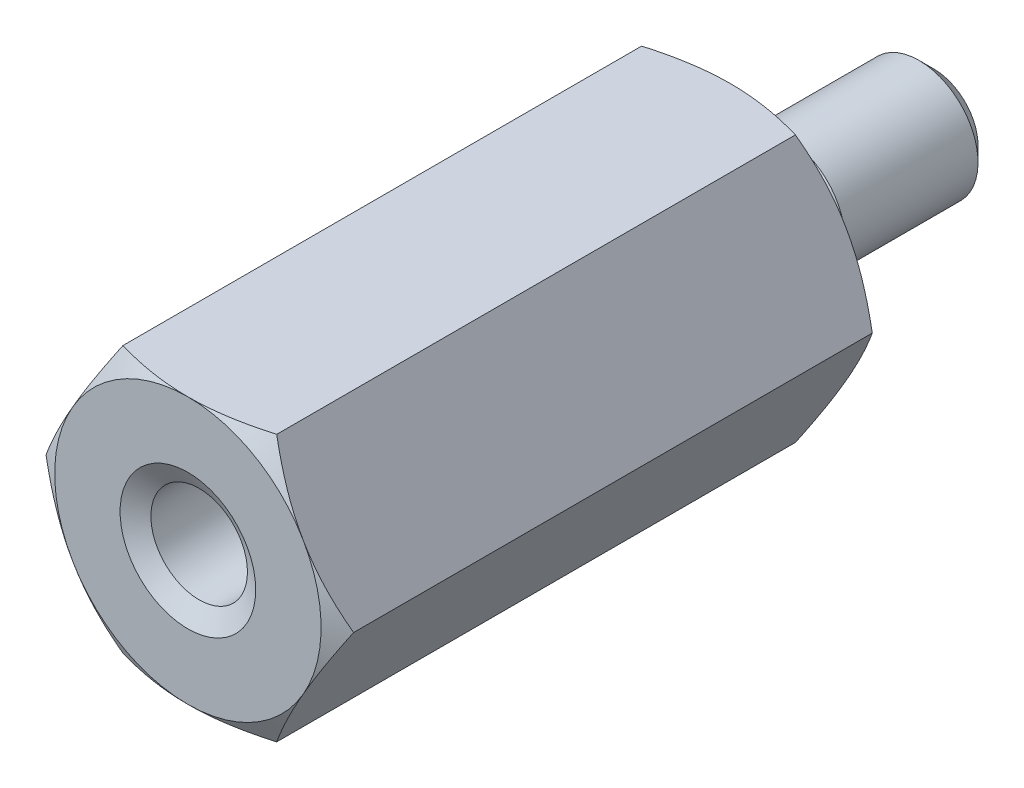
SolidWorks part; units mm, degrees
material "Plain Carbon Steel"
ref_plane "Front" through (0, 0, 0) normal (0, 0, 1) x (1, 0, 0)
ref_plane "Top" through (0, 0, 0) normal (0, 1, 0) x (1, 0, 0)
ref_plane "Right" through (0, 0, 0) normal (1, 0, 0) x (0, 0, -1)
sketch "Sketch1" plane through (0, 0, 0) normal (0, 0, 1) x (1, 0, 0)
  line L1 (3.6002, 0) -> (1.8001, 3.1179)
  line L2 (1.8001, 3.1179) -> (-1.8001, 3.1179)
  line L3 (-1.8001, 3.1179) -> (-3.6002, 0)
  line L4 (-3.6002, 0) -> (-1.8001, -3.1179)
  line L5 (-1.8001, -3.1179) -> (1.8001, -3.1178)
  line L6 (1.8001, -3.1178) -> (3.6002, 0)
  circle A0 centre (0, 0) radius 3.1178 construction
  dimension "D1" = 6.2357
extrude "Extrude1" add sketch "Sketch1" along normal mid plane 12.7
sketch "Sketch3" plane through (0, 0, 0) normal (1, 0, 0) x (0, 0, -1)
  line L0 (-6.35, 0) -> (-7.4204, 0) construction
  line L1 (-6.35, 3.1179) -> (-5.4701, 4.6418)
  line L2 (-5.4701, 4.6418) -> (-6.604, 4.6419)
  line L3 (-6.604, 4.6419) -> (-6.604, 3.1179)
  line L4 (-6.604, 3.1179) -> (-6.35, 3.1179)
  line L5 (-6.35, 0) -> (-6.35, 3.1179) construction
  dimension "D1" = 30
  dimension "D2" = 0.254
  dimension "D3" = 1.524
revolve "Cut-Revolve1" cut sketch "Sketch3" angle 360 about L0
mirror "Mirror1" about plane through (0, 0, 0) normal (0, 0, 1) of "Cut-Revolve1"
sketch "Sketch2" plane through (0, 0, 0) normal (1, 0, 0) x (0, 0, -1)
  line L0 (6.35, 0) -> (0, 0) construction
  line L1 (6.35, 1.0338) -> (7.3025, 1.0338)
  line L2 (6.35, 0) -> (6.35, 3.1179) construction
  line L3 (7.3025, 1.0338) -> (7.6486, 1.3799)
  line L4 (7.6486, 1.3799) -> (10.7664, 1.3799)
  line L5 (10.7664, 1.3799) -> (11.1125, 1.0338)
  line L6 (11.1125, 1.0338) -> (11.1125, 0)
  line L7 (11.1125, 0) -> (6.35, 0)
  line L8 (6.35, 1.0338) -> (6.35, 0)
  line L9 (6.35, -3.1178) -> (6.35, 0) construction
  dimension "D1" = 2.0676
  dimension "D2" = 2.7597
  dimension "D3" = 0.9525
  dimension "D4" = 4.7625
  dimension "D5" = 45
revolve "4-40 stud" add sketch "Sketch2" angle 360 about L0
cosmetic thread "Cosmetic Thread1" parameters "D2"=2.0676
hole_wizard "#4-40 Tapped Hole1(SHALLOW)" positions "Sketch5" profile "Sketch4" tap size "#4-40" standard "Ansi Inch"
sketch "Sketch5" plane through (0, 0, 3.175) normal (0, 0, 1) x (1, 0, 0)
  point P0 (0, 0)
cosmetic thread "Cosmetic Thread2" [suppressed]
sketch "Sketch4" plane through (0, 0, 3.175) normal (1, 0, 0) x (0, -1, 0)
  line L0 (0, 0) -> (0, 6.3942)
  line L1 (0, 6.3942) -> (1.1303, 5.715)
  line L2 (1.1303, 5.715) -> (1.1303, 0.264)
  line L3 (1.1303, 0.264) -> (1.5875, 0)
  line L5 (1.5875, 0) -> (0, 0)
  line L6 (-1.1303, 0.264) -> (-1.5875, 0) construction
  line L10 (0, 6.3942) -> (-1.1303, 5.715) construction
  line L11 (0, -6.35) -> (0, 107.95) construction
  dimension "Tap Drill Dia." = 2.2606
  dimension "Tap Drill Depth" = 5.715
  dimension "Near C'Sink Dia." = 3.175
  dimension "Near C'Sink Angle" = 120
  dimension "Drill Angle" = 118
hole_wizard "#4-40 Tapped Hole1 (STANDARD DEPTH)" positions "Sketch7" profile "Sketch6" tap size "#4-40" standard "Ansi Inch"
sketch "Sketch7" plane through (0, 0, 6.35) normal (0, 0, 1) x (1, 0, 0)
  point P0 (0, 0)
sketch "Sketch6" plane through (0, 0, 6.35) normal (1, 0, 0) x (0, -1, 0)
  line L0 (0, 0) -> (0, 8.9342)
  line L1 (0, 8.9342) -> (1.1303, 8.255)
  line L2 (1.1303, 8.255) -> (1.1303, 0.264)
  line L3 (1.1303, 0.264) -> (1.5875, 0)
  line L5 (1.5875, 0) -> (0, 0)
  line L6 (-1.1303, 0.264) -> (-1.5875, 0) construction
  line L10 (0, 8.9342) -> (-1.1303, 8.255) construction
  line L11 (0, -6.35) -> (0, 107.95) construction
  dimension "Tap Drill Dia." = 2.2606
  dimension "Tap Drill Depth" = 8.255
  dimension "Near C'Sink Dia." = 3.175
  dimension "Near C'Sink Angle" = 120
  dimension "Drill Angle" = 118
cosmetic thread "Cosmetic Thread3" parameters "D1"=6.35, "D2"=2.8448
